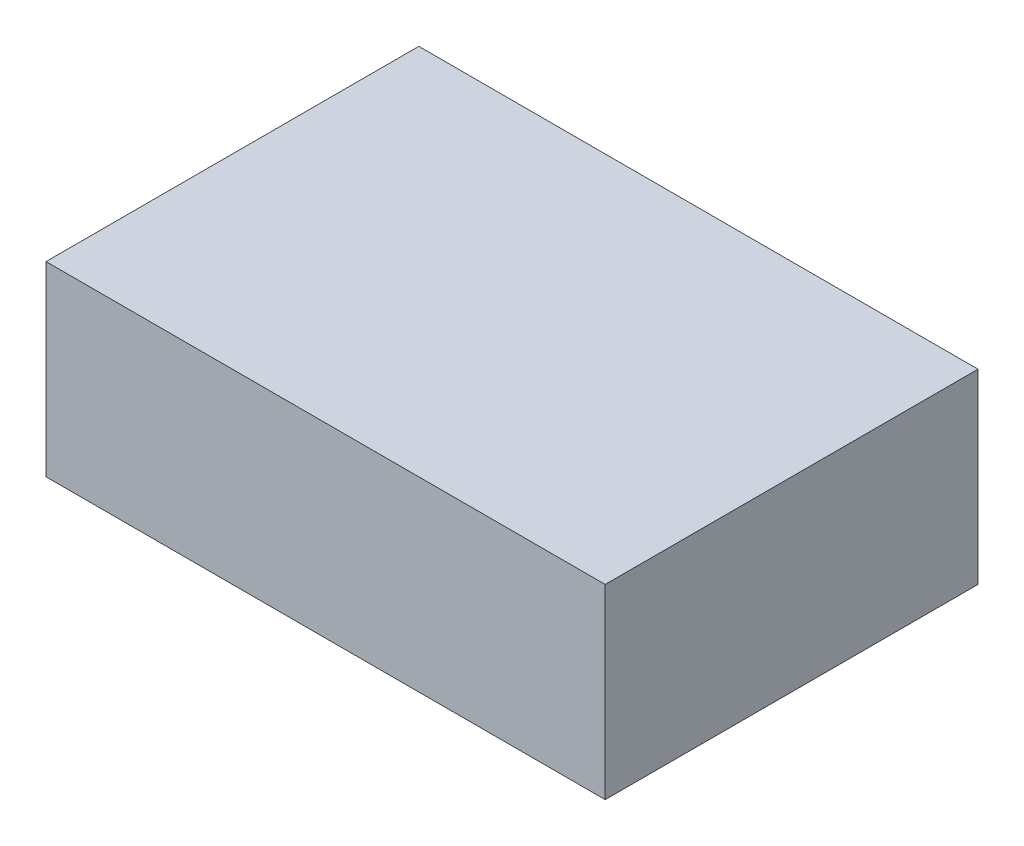
SolidWorks part; units mm, degrees
material "Rubber"
ref_plane "Front Plane" through (0, 0, 0) normal (0, 0, 1) x (1, 0, 0)
ref_plane "Top Plane" through (0, 0, 0) normal (0, 1, 0) x (1, 0, 0)
ref_plane "Right Plane" through (0, 0, 0) normal (1, 0, 0) x (0, 0, -1)
sketch "Sketch1" plane through (0, 0, 0) normal (0, 1, 0) x (1, 0, 0)
  line L1 (-152.4, 101.6) -> (152.4, 101.6)
  line L2 (-152.4, 101.6) -> (-152.4, -101.6)
  line L3 (-152.4, -101.6) -> (152.4, -101.6)
  line L4 (152.4, 101.6) -> (152.4, -101.6)
  line L5 (-152.4, 101.6) -> (152.4, -101.6) construction
  line L6 (-152.4, -101.6) -> (152.4, 101.6) construction
  point P0 (0, 0)
  dimension "D1" = 304.8
  dimension "D2" = 203.2
extrude "Boss-Extrude1" add sketch "Sketch1" along normal blind 101.6
